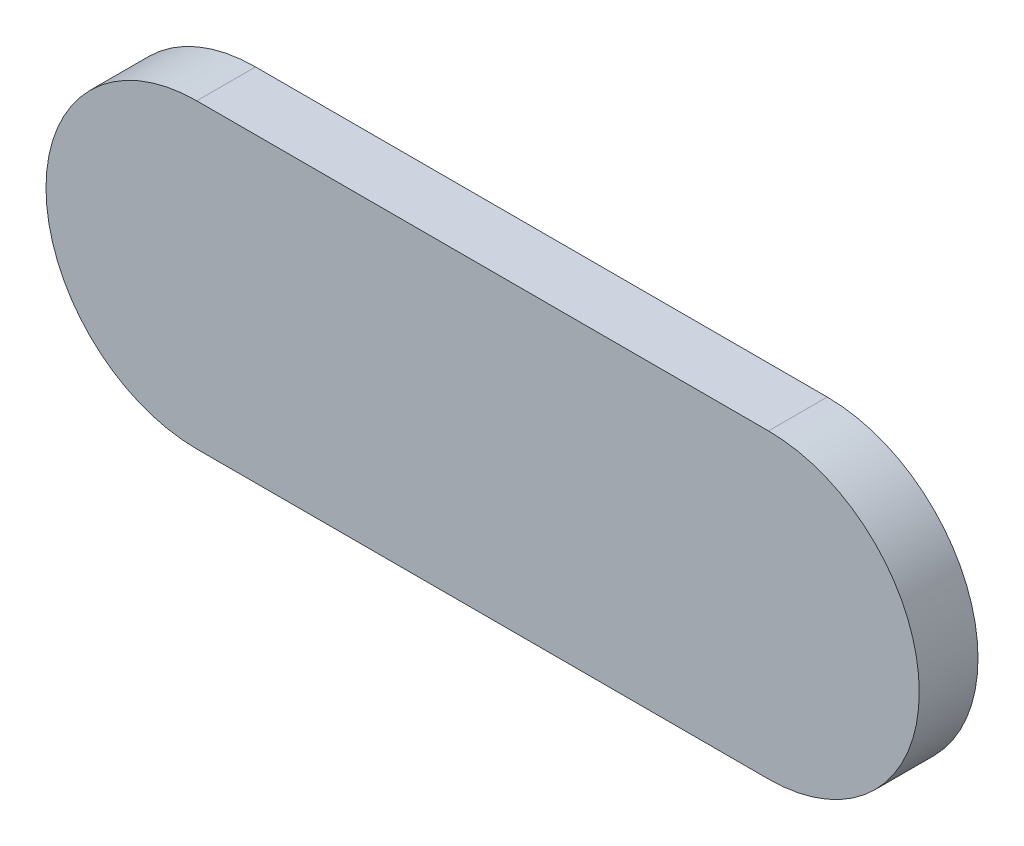
SolidWorks part; units mm, degrees
ref_plane "前视基准面" through (0, 0, 0) normal (0, 0, 1) x (1, 0, 0)
ref_plane "上视基准面" through (0, 0, 0) normal (0, 1, 0) x (1, 0, 0)
ref_plane "右视基准面" through (0, 0, 0) normal (1, 0, 0) x (0, 0, -1)
sketch "草图1" plane through (0, 0, 0) normal (0, 0, 1) x (1, 0, 0)
  line L3 (7.3, 3.85) -> (-7.3, 3.85)
  line L5 (-7.3, -3.85) -> (7.3, -3.85)
  arc A0 (7.3, -3.85) -> (7.3, 3.85) centre (7.3, 0) ccw
  arc A1 (-7.3, 3.85) -> (-7.3, -3.85) centre (-7.3, 0) ccw
extrude "凸台-拉伸1" add sketch "草图1" along normal blind 1.5
sketch "草图2" plane through (0, 0, 0) normal (0, 0, -1) x (-1, 0, 0)
  line L0 (-7.35, 2.3) -> (7.35, 2.3)
  line L1 (-7.35, -2.3) -> (7.35, -2.3)
  arc A0 (7.35, -2.3) -> (7.35, 2.3) centre (7.35, 0) ccw
  arc A1 (-7.35, -2.3) -> (-7.35, 2.3) centre (-7.35, 0) cw
extrude "凸台-拉伸2" add sketch "草图2" along normal blind 0.5
sketch "草图3" plane through (0, 0, -0.5) normal (0, 0, -1) x (-1, 0, 0)
  circle A0 centre (1.27, 0) radius 0.75
  circle A1 centre (3.81, 0) radius 0.75
  circle A2 centre (-3.81, 0) radius 0.75
  circle A3 centre (-1.27, 0) radius 0.75
extrude "凸台-拉伸3" add sketch "草图3" along normal blind 0.2
